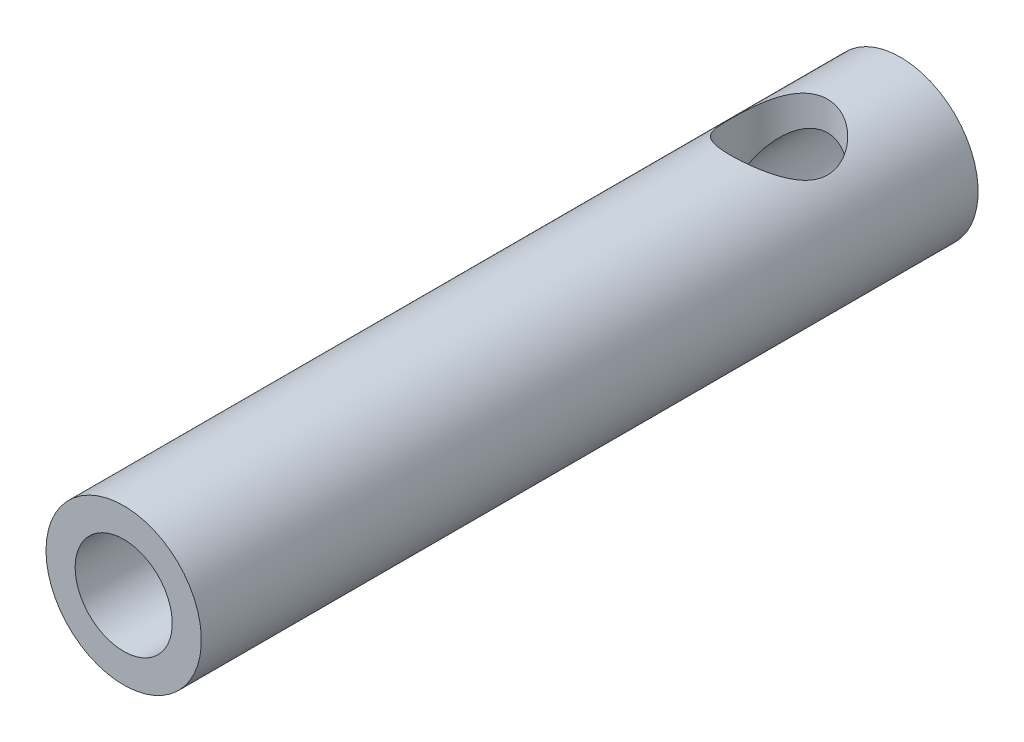
SolidWorks part; units mm, degrees
material "2014 Legierung"
ref_plane "Ebene vorne" through (0, 0, 0) normal (0, 0, 1) x (1, 0, 0)
ref_plane "Ebene oben" through (0, 0, 0) normal (0, 1, 0) x (1, 0, 0)
ref_plane "Ebene rechts" through (0, 0, 0) normal (1, 0, 0) x (0, 0, -1)
sketch "Skizze1" plane through (0, 0, 0) normal (1, 0, 0) x (0, 0, -1)
  line L0 (0, 0) -> (-32.0536, 0) construction
  line L1 (-8, 1) -> (8, 1)
  line L2 (8, 1) -> (8, 1.6)
  line L3 (8, 1.6) -> (-8, 1.6)
  line L6 (-8, 1.6) -> (-8, 1)
  line L7 (0, 1.6) -> (0, 0) construction
  dimension "D1" = 2
  dimension "D2" = 3.2
  dimension "D4" = 16
revolve "Rotation1" add sketch "Skizze1" angle 360 about L0
sketch "Skizze2" plane through (0, 0, 0) normal (0, 1, 0) x (1, 0, 0)
  line L0 (0, 8) -> (0, 5.5) construction
  line L1 (1.6, 8) -> (-1.6, 8) construction
  circle A0 centre (0, 5.5) radius 1
  dimension "D1" = 2
  dimension "D2" = 2.5
extrude "Schnitt-Linear austragen1" cut sketch "Skizze2" along normal through all
